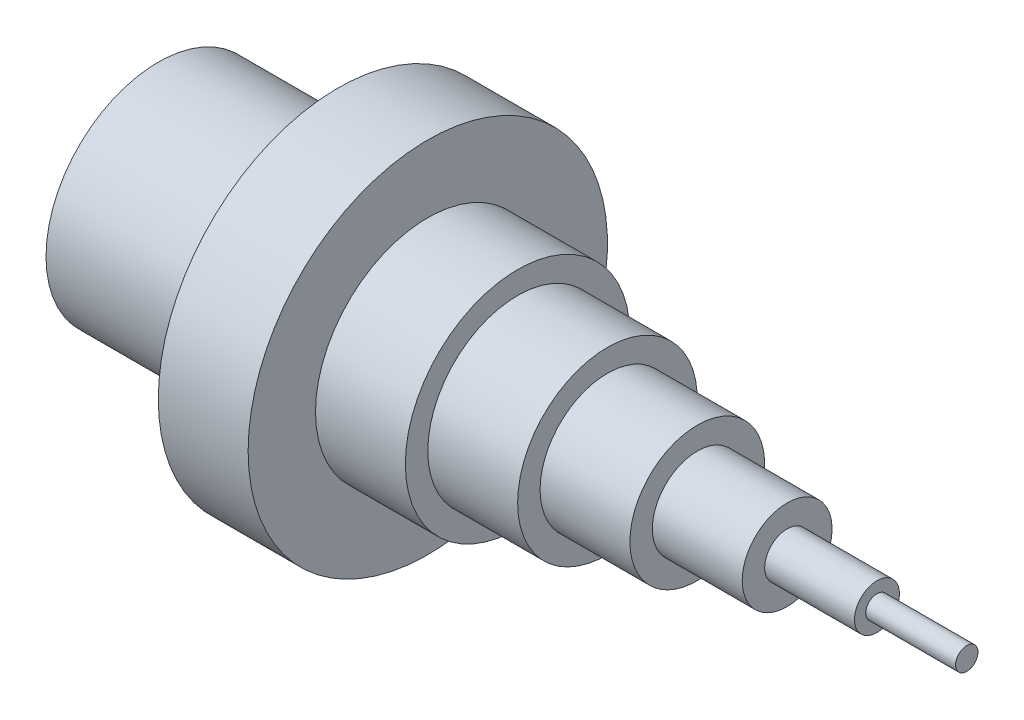
SolidWorks part; units mm, degrees
ref_plane "Front Plane" through (0, 0, 0) normal (0, 0, 1) x (1, 0, 0)
ref_plane "Top Plane" through (0, 0, 0) normal (0, 1, 0) x (1, 0, 0)
ref_plane "Right Plane" through (0, 0, 0) normal (1, 0, 0) x (0, 0, -1)
sketch "Sketch1" plane through (0, 0, 0) normal (0, 0, 1) x (1, 0, 0)
  line L0 (0, 0) -> (5350.3257, 0) construction
  line L1 (0, 0) -> (0, -635)
  line L2 (0, -635) -> (1016, -635)
  line L3 (1016, -635) -> (1016, -1016)
  line L4 (1016, -1016) -> (1524, -1016)
  line L5 (1524, -1016) -> (1524, -635)
  line L6 (1524, -635) -> (2032, -635)
  line L7 (2032, -635) -> (2032, -508)
  line L8 (2032, -508) -> (2540, -508)
  line L9 (2540, -508) -> (2540, -381)
  line L10 (2540, -381) -> (3048, -381)
  line L11 (3048, -381) -> (3048, -254)
  line L12 (3048, -254) -> (3556, -254)
  line L13 (3556, -254) -> (3556, -127)
  line L14 (3556, -127) -> (4064, -127)
  line L15 (4064, -127) -> (4064, -63.5)
  line L16 (4064, -63.5) -> (4572, -63.5)
  line L17 (4572, -63.5) -> (4572, 0)
  line L18 (0, 0) -> (4572, 0)
  dimension "D1" = 1016
  dimension "D2" = 2032
  dimension "D3" = 1270
  dimension "D4" = 1016
  dimension "D5" = 762
  dimension "D6" = 508
  dimension "D7" = 508
  dimension "D8" = 4572
  dimension "D9" = 254
  dimension "D10" = 127
revolve "Revolve1" add sketch "Sketch1" angle 360 about L0
sketch "Sketch2" plane through (0, 0, 0) normal (-1, 0, 0) x (0, 0, 1)
  circle A0 centre (0, 0) radius 508
  dimension "D1" = 1016
extrude "Cut-Extrude2" cut sketch "Sketch2" against normal blind 1016
